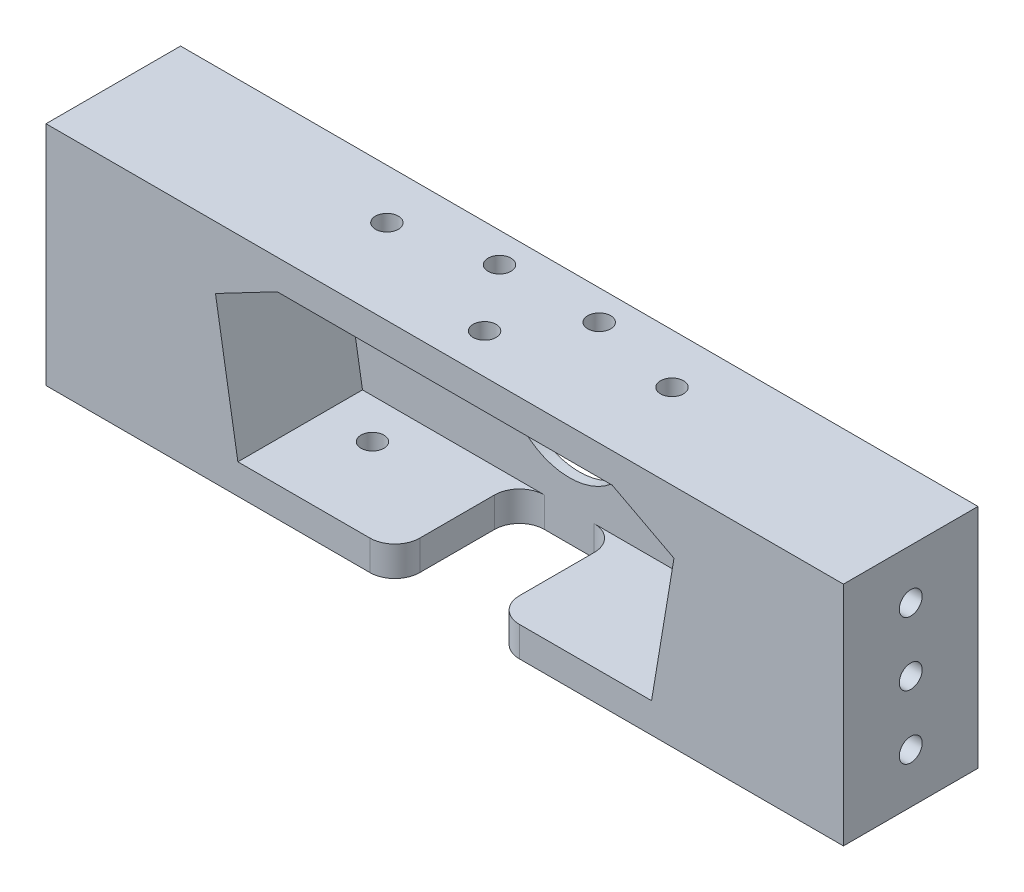
SolidWorks part; units mm, degrees
ref_plane "Alzado" through (0, 0, 0) normal (0, 0, 1) x (1, 0, 0)
ref_plane "Planta" through (0, 0, 0) normal (0, 1, 0) x (1, 0, 0)
ref_plane "Vista lateral" through (0, 0, 0) normal (1, 0, 0) x (0, 0, -1)
sketch "Croquis1" plane through (0, 0, 0) normal (0, 0, 1) x (1, 0, 0)
  line L0 (-33.6004, 16.75) -> (33.6004, 16.75)
  line L1 (-80, 22.75) -> (80, 22.75)
  line L2 (-80, 22.75) -> (-80, -22.75)
  line L3 (-80, -22.75) -> (80, -22.75)
  line L4 (80, 22.75) -> (80, -22.75)
  line L5 (-80, 22.75) -> (80, -22.75) construction
  line L6 (-80, -22.75) -> (80, 22.75) construction
  line L7 (33.6004, 16.75) -> (46, 10.25)
  line L8 (46, 10.25) -> (41.5, -16.75)
  line L9 (41.5, -16.75) -> (-41.5, -16.75)
  line L10 (-41.5, -16.75) -> (-46, 10.25)
  line L11 (-46, 10.25) -> (-33.6004, 16.75)
  point P0 (0, 0)
  dimension "D13" = 6
  dimension "D1" = 160
  dimension "D2" = 45.5
  dimension "D3" = 6
  dimension "D4" = 92
  dimension "D5" = 6.5
  dimension "D6" = 14
  dimension "D7" = 14
  dimension "D8" = 4.5
  dimension "D9" = 6.5
  dimension "D10" = 4.5
  dimension "D11" = 34
  dimension "D12" = 33.5
  dimension "D14" = 34
extrude "Saliente-Extruir1" add sketch "Croquis1" along normal blind 25
sketch "Croquis2" plane through (0, 0, 0) normal (0, 0, -1) x (-1, 0, 0)
  line L0 (-80, 22.75) -> (-80, -22.75)
  line L1 (-80, -22.75) -> (80, -22.75)
  line L2 (80, -22.75) -> (80, 22.75)
  line L3 (80, 22.75) -> (-80, 22.75)
extrude "Saliente-Extruir2" add sketch "Croquis2" along normal blind 2
sketch "Croquis5" plane through (0, 0, 0) normal (0, 0, 1) x (1, 0, 0)
  line L0 (33.6004, 16.75) -> (-33.6004, 16.75) construction
  circle A0 centre (0, 1.75) radius 13
  point P4 (0, 16.75)
  point P5 (0, 1.75)
  dimension "D3" = 26
  dimension "D1" = 15
  dimension "D2" = 0
extrude "Cortar-Extruir3" cut sketch "Croquis5" against normal blind 2
sketch "Croquis6" plane through (0, -16.75, 0) normal (0, 1, 0) x (1, 0, 0)
  line L0 (-41.5, -25) -> (41.5, -25) construction
  line L1 (-10, 0) -> (10, 0)
  line L2 (-10, 0) -> (-10, -25)
  line L3 (-10, -25) -> (10, -25)
  line L4 (10, 0) -> (10, -25)
  line L5 (-41.5, 0) -> (41.5, 0) construction
  point P6 (0, 0)
  point P9 (0, 0)
  dimension "D1" = 0
  dimension "D2" = 20
extrude "Cortar-Extruir4" cut sketch "Croquis6" against normal up to next
fillet "Redondeo1" radius 5 2 edges at (10, -19.75, 0) (-10, -19.75, 0)
fillet "Redondeo2" radius 5 2 edges at (10, -19.75, 25) (-10, -19.75, 25)
sketch "Croquis7" plane through (0, -16.75, 0) normal (0, 1, 0) x (1, 0, 0)
  line L0 (-41.5, -25) -> (-41.5, 0) construction
  line L1 (41.5, -25) -> (41.5, 0) construction
  line L2 (-41.5, 0) -> (-5, 0) construction
  line L3 (5, 0) -> (41.5, 0) construction
  circle A0 centre (-31.5, -8) radius 2.3
  circle A1 centre (31.5, -8) radius 2.3
  dimension "D5" = 4.6
  dimension "D6" = 4.6
  dimension "D1" = 10
  dimension "D2" = 10
  dimension "D3" = 8
  dimension "D4" = 8
extrude "Cortar-Extruir5" cut sketch "Croquis7" against normal up to next
sketch "Croquis8" plane through (0, 16.75, 0) normal (0, -1, 0) x (1, 0, 0)
  line L0 (33.6004, 0) -> (-33.6004, 0) construction
  line L1 (-33.6004, 25) -> (-33.6004, 0) construction
  line L2 (33.6004, 25) -> (33.6004, 0) construction
  circle A0 centre (-28.6004, 8) radius 2.3
  circle A1 centre (28.6004, 8) radius 2.3
  dimension "D5" = 4.6
  dimension "D6" = 4.6
  dimension "D1" = 8
  dimension "D2" = 8
  dimension "D3" = 5
  dimension "D4" = 5
extrude "Cortar-Extruir6" cut sketch "Croquis8" against normal up to next
sketch "Croquis9" plane through (0, 22.75, 0) normal (0, 1, 0) x (1, 0, 0)
  line L0 (-80, 2) -> (80, 2) construction
  circle A0 centre (-10, -4) radius 2.3
  circle A1 centre (10, -4) radius 2.3
  circle A2 centre (0, -17) radius 2.3
  point P8 (0, 2)
  dimension "D3" = 4.6
  dimension "D4" = 4.6
  dimension "D5" = 4.6
  dimension "D1" = 6
  dimension "D2" = 6
  dimension "D6" = 20
  dimension "D7" = 10
  dimension "D8" = 13
  dimension "D9" = 10
extrude "Cortar-Extruir7" cut sketch "Croquis9" against normal up to next
sketch "Croquis10" plane through (-80, 0, 0) normal (-1, 0, 0) x (0, 0, 1)
  line L0 (-2, -22.75) -> (-2, 22.75) construction
  line L2 (25, -22.75) -> (-2, -22.75) construction
  line L3 (25, 22.75) -> (-2, 22.75) construction
  circle A0 centre (11.5, 0) radius 2.3
  circle A1 centre (11.5, -12.75) radius 2.3
  circle A2 centre (11.5, 12.75) radius 2.3
  dimension "D2" = 4.6
  dimension "D3" = 4.6
  dimension "D5" = 4.6
  dimension "D1" = 13.5
  dimension "D4" = 13.5
  dimension "D6" = 13.5
  dimension "D7" = 10
  dimension "D8" = 10
  dimension "D9" = 12.75
extrude "Cortar-Extruir8" cut sketch "Croquis10" against normal blind 20
sketch "Croquis11" plane through (80, 0, 0) normal (1, 0, 0) x (0, 0, -1)
  line L0 (2, 22.75) -> (2, -22.75) construction
  line L1 (-25, -22.75) -> (2, -22.75) construction
  line L2 (-25, 22.75) -> (2, 22.75) construction
  circle A0 centre (-11.5, 12.75) radius 2.3
  circle A1 centre (-11.5, 0) radius 2.3
  circle A2 centre (-11.5, -12.75) radius 2.3
  dimension "D1" = 4.6
  dimension "D2" = 4.6
  dimension "D3" = 4.6
  dimension "D4" = 13.5
  dimension "D5" = 13.5
  dimension "D6" = 13.5
  dimension "D7" = 10
  dimension "D8" = 10
  dimension "D9" = 12.75
extrude "Cortar-Extruir9" cut sketch "Croquis11" against normal blind 20
